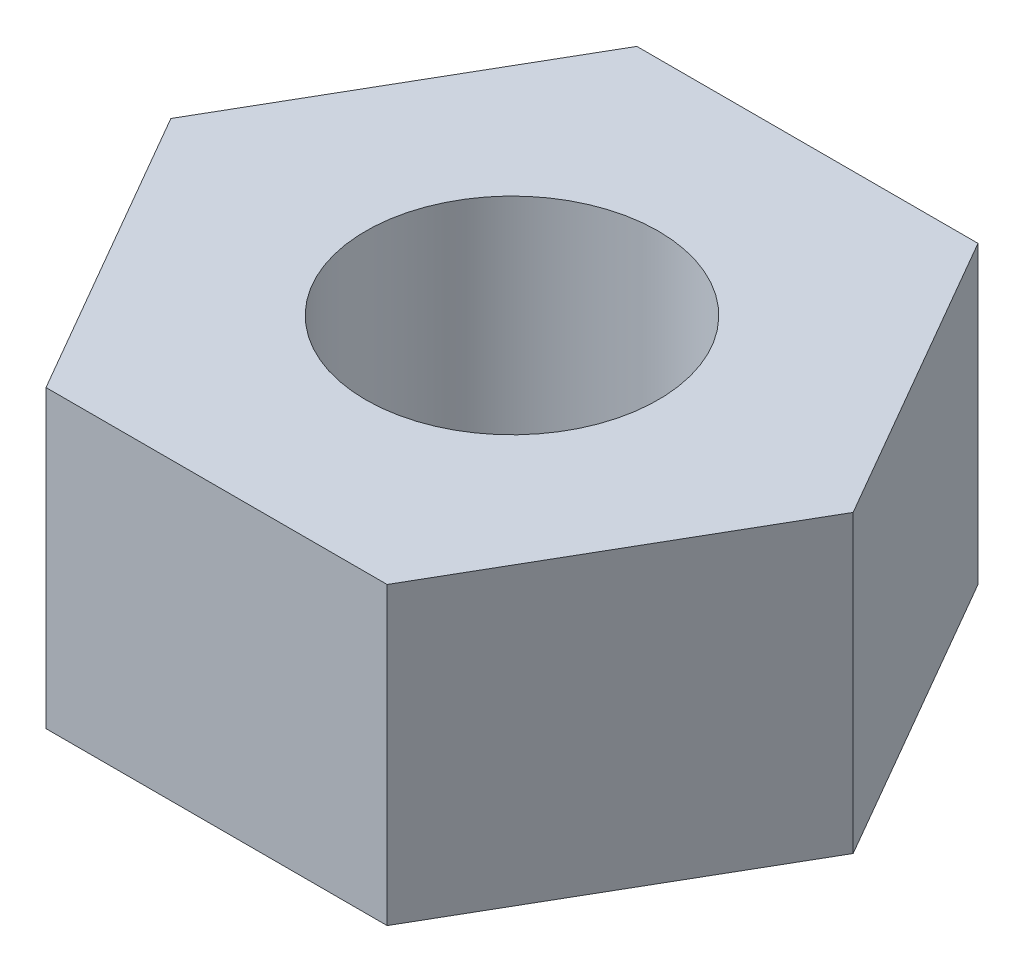
SolidWorks part; units mm, degrees
ref_plane "Front Plane" through (0, 0, 0) normal (0, 0, 1) x (1, 0, 0)
ref_plane "Top Plane" through (0, 0, 0) normal (0, 1, 0) x (1, 0, 0)
ref_plane "Right Plane" through (0, 0, 0) normal (1, 0, 0) x (0, 0, -1)
sketch "Sketch1" plane through (0, 0, 0) normal (0, 1, 0) x (1, 0, 0)
  line L1 (2.3094, 0) -> (1.1547, 2)
  line L2 (1.1547, 2) -> (-1.1547, 2)
  line L3 (-1.1547, 2) -> (-2.3094, 0)
  line L4 (-2.3094, 0) -> (-1.1547, -2)
  line L5 (-1.1547, -2) -> (1.1547, -2)
  line L6 (1.1547, -2) -> (2.3094, 0)
  circle A1 centre (0, 0) radius 2 construction
  point P1 (-3.8572, 9.4083)
  dimension "D2" = 2
extrude "Boss-Extrude1" add sketch "Sketch1" along normal blind 2
sketch "Sketch2" plane through (0, 0, 0) normal (0, 1, 0) x (1, 0, 0)
  circle A0 centre (0, 0) radius 0.99
  dimension "D1" = 1.98
extrude "Cut-Extrude1" cut sketch "Sketch2" along normal through all
sketch "Sketch3" plane through (0, 0, 0) normal (0, 1, 0) x (1, 0, 0)
  circle A1 centre (0, 0) radius 0.9931
curve "Helix/Spiral1" pitch 0.25 height 2 turns 8
